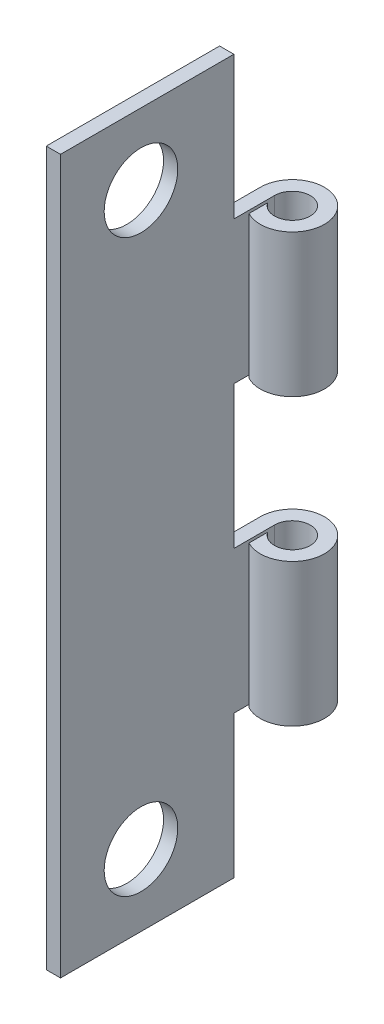
SolidWorks part; units mm, degrees
ref_plane "Front Plane" through (0, 0, 0) normal (0, 0, 1) x (1, 0, 0)
ref_plane "Top Plane" through (0, 0, 0) normal (0, 1, 0) x (1, 0, 0)
ref_plane "Right Plane" through (0, 0, 0) normal (1, 0, 0) x (0, 0, -1)
sketch "Sketch1" plane through (0, 0, 0) normal (1, 0, 0) x (0, 0, -1)
  line L0 (0, 0) -> (0, 31.75) construction
  line L1 (0, 0) -> (9.525, 0) construction
  line L2 (4.3053, 3.175) -> (7.5819, 3.175) construction
  line L3 (0, 0) -> (-9.525, 0) construction
  point P3 (5.9436, 3.175)
  point P5 (5.9436, 28.575)
  point P6 (0, 6.35)
  point P9 (-101.6, 31.75)
  point P10 (5.9436, 3.175)
  point P11 (-25.4, 31.75)
  point P12 (-127, 31.75)
  point P13 (-5.9436, 28.575)
  point P14 (-5.9436, 3.175)
  dimension "Knuckle Length" = 6.35
  dimension "Length Corner" = 3.175
  dimension "Height Corner" = 3.5814
  dimension "Overall Width" = 19.05
  dimension "Leaf Height" = 31.75
  dimension "MTG Dia" = 3.2766
  dimension "D1" = 3.175
  dimension "Num Holes" = 101.6
  dimension "Spring Knuckles" = 25.4
  dimension "Num Knuckles" = 127
  dimension "D2" = 3.5814
  dimension "Length Corner 2" = 3.175
  dimension "D4" = 3.175
sketch "Sketch2" plane through (0, 0, 0) normal (0, 1, 0) x (1, 0, 0)
  line L0 (0.635, 0) -> (2.2225, 0) construction
  line L1 (0, 9.525) -> (0.635, 9.525) construction
  line L2 (-0.6096, 9.3027) -> (0, 9.3027) construction
  line L3 (1.4288, 0.7937) -> (1.4288, 1.4287) construction
  line L5 (1.4288, 1.4287) -> (1.4288, 9.3027) construction
  circle A0 centre (1.4288, 0) radius 0.7938 construction
  point P9 (1.4288, 0.8191)
  point P10 (0.762, 9.3027)
  dimension "Leaf Thickness" = 0.635
  dimension "Pin Dia" = 1.5875
  dimension "Wire Dia" = 0.6096
  dimension "Spring Leg Length" = 7.874
  dimension "Bend Clearence" = 0.127
  dimension "D1" = 0.6096
  dimension "Open Close Offset" = 1.3716
sketch "Sketch4" plane through (0, 0, 0) normal (0, 1, 0) x (1, 0, 0)
  line L0 (0, 0) -> (0, -9.525)
  line L1 (0, -9.525) -> (0.635, -9.525)
  line L2 (0.635, -9.525) -> (0.635, 0)
  line L3 (0.762, -0.4307) -> (0.762, -1.2636)
  line L4 (0.635, 0) -> (2.2225, 0) construction
  line L5 (0, 0) -> (0, 9.525) construction
  arc A0 (0.762, -1.2636) -> (0, 0) centre (1.4288, 0) ccw
  arc A1 (0.762, -0.4307) -> (0.635, 0) centre (1.4288, 0) ccw
extrude "Boss-Extrude2" add sketch "Sketch4" along normal up to vertex (31.75 mm away) separate body up to point (0, 31.75, 0)
sketch "Sketch7" plane through (0, 0, 0) normal (1, 0, 0) x (0, 0, -1)
  line L0 (-1.8098, 38.1) -> (1.8097, 38.1)
  line L1 (-1.8098, 12.7) -> (1.8097, 12.7)
  line L2 (-1.8098, 12.7) -> (-1.8097, 6.35)
  line L3 (-1.8097, 6.35) -> (1.8098, 6.35)
  line L4 (1.8097, 12.7) -> (1.8098, 6.35)
  line L5 (-1.8098, 25.4) -> (1.8097, 25.4)
  line L6 (-1.8098, 25.4) -> (-1.8097, 19.05)
  line L7 (1.8097, 25.4) -> (1.8098, 19.05)
  line L8 (-1.8097, 19.05) -> (1.8098, 19.05)
  line L9 (-1.8098, 12.7) -> (-1.8098, 25.4) construction
  line L10 (-1.8098, 38.1) -> (-1.8097, 31.75)
  line L11 (1.8097, 38.1) -> (1.8098, 31.75)
  line L12 (-1.8097, 31.75) -> (1.8098, 31.75)
  point P5 (0, 6.35)
  dimension "D1" = 6.35
  dimension "D2" = 3.6195
  dimension "D4" = 12.7
  dimension "D3" = 3
sketch "Sketch8" plane through (0, 0, 0) normal (1, 0, 0) x (0, 0, -1)
  line L0 (-1.8097, 6.35) -> (1.8098, 6.35) construction
  line L1 (-1.8097, 6.35) -> (1.8098, 6.35)
  line L2 (-1.8097, 6.35) -> (-1.8098, 0)
  line L3 (-1.8098, 0) -> (1.8098, 0)
  line L4 (1.8098, 6.35) -> (1.8098, 0)
  line L5 (-1.8098, 12.7) -> (-1.8097, 6.35) construction
  line L6 (-1.8097, 19.05) -> (1.8098, 19.05)
  line L7 (-1.8097, 19.05) -> (-1.8098, 12.7)
  line L8 (-1.8098, 12.7) -> (1.8098, 12.7)
  line L9 (1.8098, 19.05) -> (1.8098, 12.7)
  line L10 (-1.8097, 6.35) -> (-1.8097, 19.05) construction
  line L11 (-1.8097, 31.75) -> (1.8098, 31.75)
  line L12 (-1.8097, 31.75) -> (-1.8098, 25.4)
  line L13 (-1.8098, 25.4) -> (1.8098, 25.4)
  line L14 (1.8098, 31.75) -> (1.8098, 25.4)
  dimension "D2" = 12.7
  dimension "D1" = 3
extrude "Cut-Extrude3" cut sketch "Sketch8" along normal through all
ref_plane "Plane1" through (0, 13.0048, 0) normal (0, 1, 0) x (1, 0, 0)
ref_plane "Plane2" through (0, 18.7452, 0) normal (0, 1, 0) x (1, 0, 0)
sketch "Sketch15" plane through (0, 0, 0) normal (1, 0, 0) x (0, 0, -1)
  circle A1 centre (-5.9436, 3.175) radius 1.6383
  dimension "D1" = 3.2766
extrude "Cut-Extrude5" cut sketch "Sketch15" along normal through all
ref_plane "Plane3" through (0, 15.875, 0) normal (0, -1, 0) x (-1, 0, 0)
mirror "Mirror1" about plane through (0, 15.875, 0) normal (0, -1, 0) of "Cut-Extrude5"
equation "\"Num Knuckles\"=5"
equation "\"D1@Sketch7\"=\"Knuckle Length@Sketch1\""
equation "\"D2@Sketch7\" = ( 2 * \"Leaf Thickness@Sketch2\" ) + \"Pin Dia@Sketch2\" + ( .04 * \"Overall Width@Sketch1\" )"
equation "\"D4@Sketch7\"=\"Knuckle Length@Sketch1\"*2"
equation "\"D3@Sketch7\" = int ( \"Num Knuckles@Sketch1\" / 2 )  + 1"
equation "\"D2@Sketch8\"=\"D4@Sketch7\""
equation "\"D1@Sketch8\"=\"D3@Sketch7\""
equation "\"Spring Knuckles\"= 1"
equation "\"Num Holes\"=4"
equation "\"D1@Sketch1\"= \"Length Corner@Sketch1\""
equation "\"D1@Sketch2\"= \"Wire Dia@Sketch2\""
equation "\"Knuckle Length@Sketch1\"=\"Leaf Height@Sketch1\"/\"Num Knuckles@Sketch1\""
equation "\"D2@Sketch1\"=\"Height Corner@Sketch1\""
equation "\"D4@Sketch1\" = \"Length Corner 2@Sketch1\""
